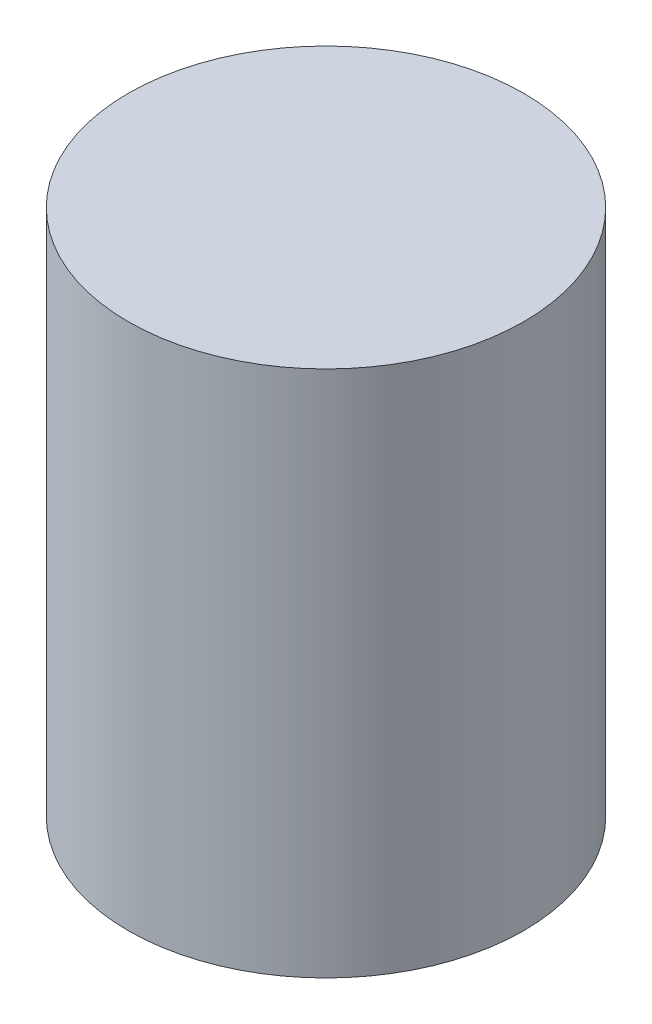
SolidWorks part; units mm, degrees
ref_plane "Front Plane" through (0, 0, 0) normal (0, 0, 1) x (1, 0, 0)
ref_plane "Top Plane" through (0, 0, 0) normal (0, 1, 0) x (1, 0, 0)
ref_plane "Right Plane" through (0, 0, 0) normal (1, 0, 0) x (0, 0, -1)
sketch "Sketch1" plane through (0, 0, 0) normal (0, 1, 0) x (1, 0, 0)
  circle A0 centre (0, 0) radius 1.5
  dimension "3" = 3
extrude "Boss-Extrude1" add sketch "Sketch1" along normal blind 4
